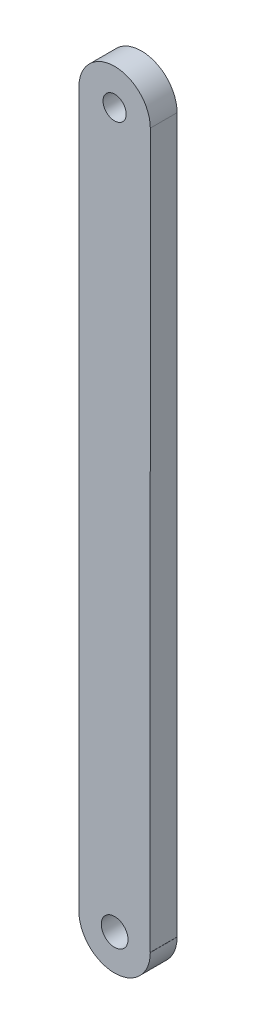
SolidWorks part; units mm, degrees
ref_plane "Front Plane" through (0, 0, 0) normal (0, 0, 1) x (1, 0, 0)
ref_plane "Top Plane" through (0, 0, 0) normal (0, 1, 0) x (1, 0, 0)
ref_plane "Right Plane" through (0, 0, 0) normal (1, 0, 0) x (0, 0, -1)
sketch "Model" plane through (0, 0, 0) normal (0, 0, 1) x (1, 0, 0)
  line L1 (47.5001, 80.0001) -> (47.5001, 0)
  line L2 (55.4838, 0) -> (55.4999, 0)
  line L3 (55.4999, 80.0001) -> (55.4838, 0)
  circle A0 centre (51.5001, 0) radius 1.5
  circle A1 centre (51.5001, 80) radius 1.3
  arc A2 (55.4999, 80.0001) -> (47.5001, 80.0001) centre (51.5, 80.0001) ccw
  arc A3 (47.5001, 0) -> (55.4999, 0) centre (51.5, 0) ccw
extrude "Boss-Extrude1" add sketch "Model" along normal blind 3
